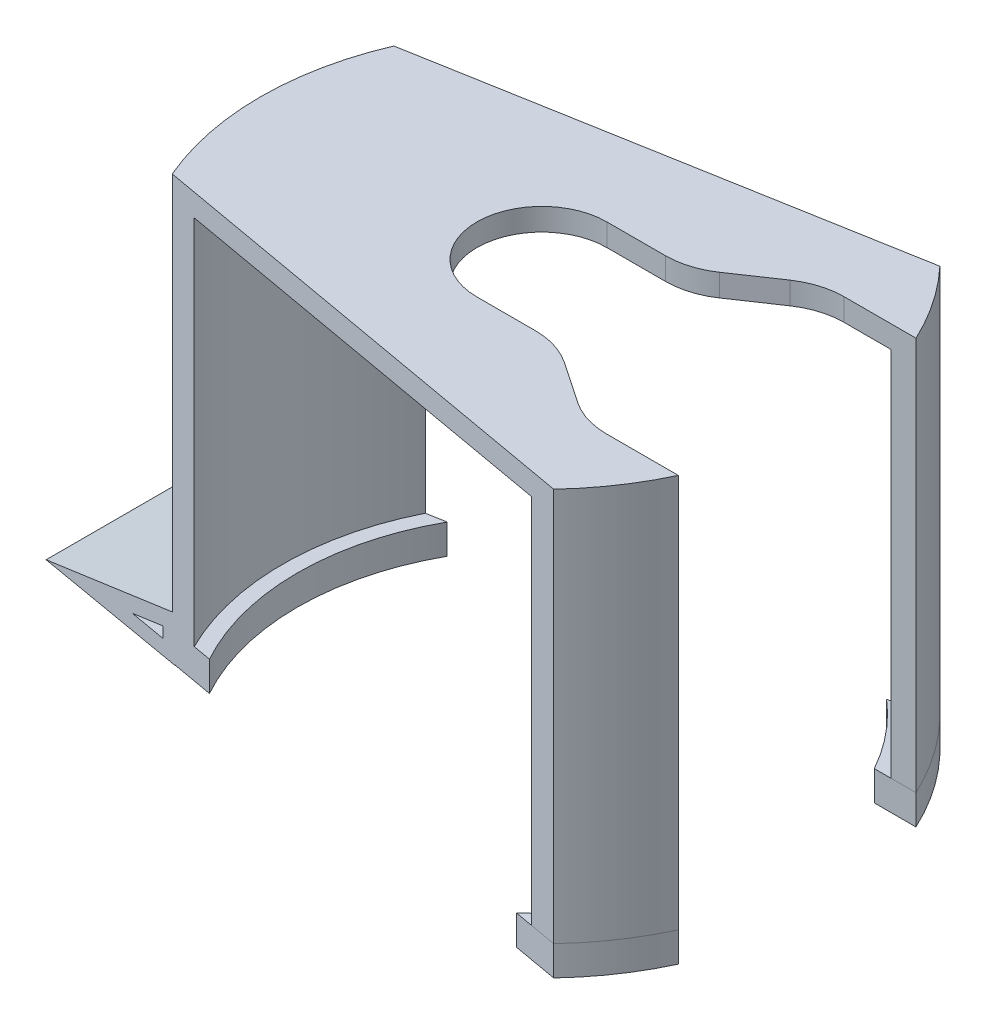
SolidWorks part; units mm, degrees
ref_plane "Front Plane" through (0, 0, 0) normal (0, 0, 1) x (1, 0, 0)
ref_plane "Top Plane" through (0, 0, 0) normal (0, 1, 0) x (1, 0, 0)
ref_plane "Right Plane" through (0, 0, 0) normal (1, 0, 0) x (0, 0, -1)
sketch "Sketch1" plane through (0, 0, 0) normal (0, 1, 0) x (1, 0, 0)
  line L0 (-34.3681, 16) -> (34.3681, 16)
  line L1 (0, 0) -> (-37.91, 0) construction
  line L2 (-34.3681, -16) -> (34.3681, -16)
  line L3 (27.5893, 26) -> (23.2961, 26)
  line L4 (27.5893, -26) -> (23.2961, -26)
  circle A0 centre (0, 0) radius 37.91
  circle A1 centre (0, 0) radius 34.91
  dimension "D1" = 69.82
  dimension "D2" = 3
  dimension "D3" = 32
  dimension "D4" = 10
extrude "Boss-Extrude1" add sketch "Sketch1" along normal blind 50 contours A1 L0 A0 L3 | A1 L4 A0 L2 | A1 L1 A0 L2 | L1 A1 L0 A0
sketch "Sketch2" plane through (0, 0, 0) normal (0, 1, 0) x (1, 0, 0)
  line L0 (34.3681, 16) -> (-34.3681, 16)
  line L1 (-34.3681, 16) -> (-31.0275, 16) construction
  line L2 (34.3681, -16) -> (-34.3681, -16)
  line L3 (27.5893, 26) -> (20.1759, 26)
  line L4 (27.5893, -26) -> (20.1759, -26)
  line L5 (27.5893, -26) -> (23.2961, -26) construction
  line L6 (-34.3681, -16) -> (-31.0275, -16) construction
  circle A0 centre (0, 0) radius 32.91
  circle A1 centre (0, 0) radius 37.91
  arc A2 (-34.3681, 16) -> (-34.3681, -16) centre (0, 0) ccw construction
  dimension "D1" = 65.82
extrude "Boss-Extrude2" add sketch "Sketch2" against normal blind 4 contours L0 A1 L2 A0 | L0 A1 L3 A0 | L4 A1 L2 A0
sketch "Sketch3" plane through (0, 0, 16) normal (0, 0, 1) x (1, 0, 0)
  line L0 (-34.3681, -4.0483) -> (-55.4988, -4.145)
  line L1 (-55.4988, -4.145) -> (-34.3681, 2.0732)
  line L3 (-34.3681, 2.0732) -> (-34.3681, -4.0483)
  line L4 (-36.3681, -2.0574) -> (-41.3985, -2.0804)
  line L5 (-41.3985, -2.0804) -> (-36.3681, -0.6001)
  line L6 (-36.3681, -0.6001) -> (-36.3681, -2.0574)
  line L8 (-34.3681, 50) -> (-34.3681, -4) construction
  dimension "D1" = 2
extrude "Boss-Extrude3" add sketch "Sketch3" against normal up to surface (32 mm away)
sketch "Sketch4" plane through (0, 50, 0) normal (0, 1, 0) x (1, 0, 0)
  line L0 (27.5893, 26) -> (-55.4988, 11.2545)
  line L1 (-55.4988, 16) -> (-55.4988, -16) construction
  line L2 (-55.4988, 0) -> (-65.642, 0) construction
  line L3 (27.5893, -26) -> (-55.4988, -11.2545)
  line L4 (-55.4988, 11.2545) -> (-55.4988, -11.2545)
  line L5 (27.5893, -26) -> (27.5893, -30.8155)
  line L6 (27.5893, -30.8155) -> (-65.642, -30.8155)
  line L7 (-65.642, -30.8155) -> (-65.0732, 32.7339)
  line L8 (-65.0732, 32.7339) -> (27.5893, 31.9044)
  line L9 (27.5893, 31.9044) -> (27.5893, 26)
extrude "Cut-Extrude1" cut sketch "Sketch4" against normal blind 58
sketch "Sketch5" plane through (0, 50, 0) normal (0, 1, 0) x (1, 0, 0)
  line L0 (0, 8.75) -> (7.8686, 8.75)
  line L2 (27.5893, 26) -> (-34.8511, 14.9188)
  line L3 (-55.4988, 0) -> (41.4633, 0) construction
  line L4 (-55.4988, 11.2545) -> (-55.4988, -11.2545) construction
  line L5 (27.5893, -26) -> (-34.8511, -14.9188)
  line L7 (0, -8.75) -> (7.8686, -8.75)
  line L8 (34.3681, -16) -> (24.7108, -16)
  line L9 (19.1046, -14.2807) -> (13.4748, -10.4693)
  line L10 (19.1046, 14.2807) -> (13.4748, 10.4693)
  line L11 (34.3681, 16) -> (24.7108, 16)
  arc A0 (0, 8.75) -> (0, -8.75) centre (0, 0) ccw
  arc A1 (-34.8511, 14.9188) -> (-34.8511, -14.9188) centre (0, 0) ccw
  arc A2 (27.5893, -26) -> (34.3681, -16) centre (0, 0) ccw
  arc A5 (34.3681, 16) -> (27.5893, 26) centre (0, 0) ccw
  arc A6 (7.8686, 8.75) -> (13.4748, 10.4693) centre (7.8686, 18.75) ccw
  arc A7 (13.4748, -10.4693) -> (7.8686, -8.75) centre (7.8686, -18.75) ccw
  arc A8 (24.7108, -16) -> (19.1046, -14.2807) centre (24.7108, -6) cw
  arc A9 (19.1046, 14.2807) -> (24.7108, 16) centre (24.7108, 6) cw
  point P28 (10.9353, 8.75)
  point P31 (10.9353, -8.75)
  point P34 (21.6441, -16)
  point P37 (21.6441, 16)
  dimension "D1" = 17.5
  dimension "D2" = 10
extrude "Boss-Extrude4" add sketch "Sketch5" along normal blind 3
sketch "Sketch6" plane through (0, 0, 0) normal (0, 1, 0) x (1, 0, 0)
  circle A0 centre (0, 0) radius 34.91
extrude "Cut-Extrude2" cut sketch "Sketch6" along normal blind 10
sketch "Sketch7" plane through (0, 0, 0) normal (0, 0, 1) x (1, 0, 0)
  line L0 (0, 0) -> (-34.91, 0) construction
  line L5 (-31.2517, 0) -> (-34.91, 0) construction
  line L8 (-34.91, 4.3364) -> (-32.91, 4.3364)
  line L9 (-32.91, 4.3364) -> (-34.91, 8.3364)
  line L10 (-34.91, 8.3364) -> (-34.91, 4.3364)
  dimension "D1" = 2
  dimension "D2" = 4
